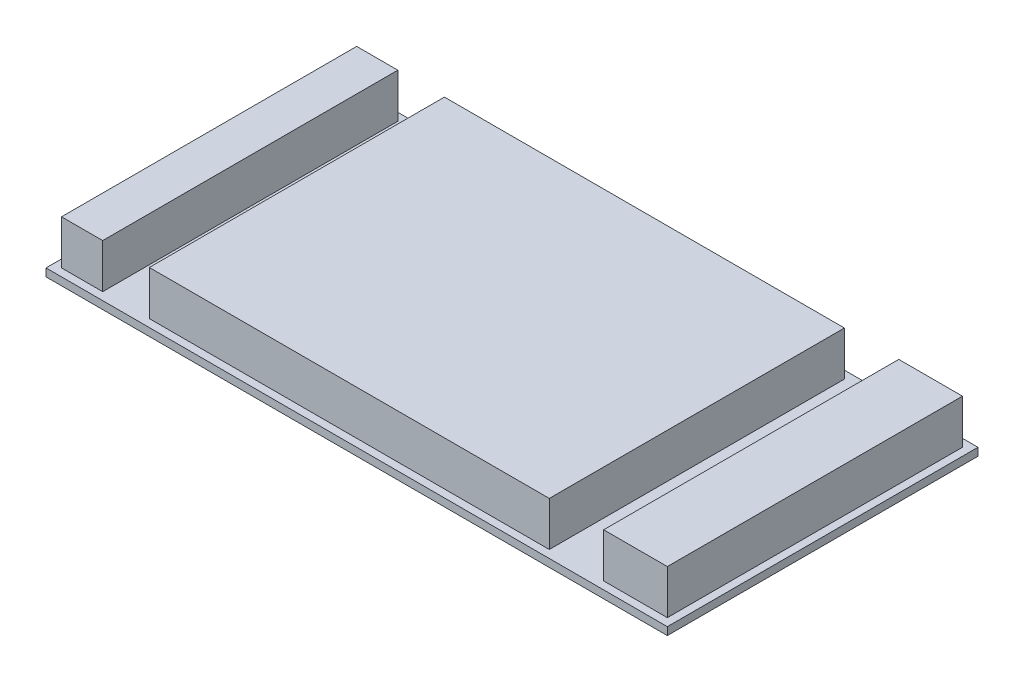
SolidWorks part; units mm, degrees
ref_plane "Front Plane" through (0, 0, 0) normal (0, 0, 1) x (1, 0, 0)
ref_plane "Top Plane" through (0, 0, 0) normal (0, 1, 0) x (1, 0, 0)
ref_plane "Right Plane" through (0, 0, 0) normal (1, 0, 0) x (0, 0, -1)
sketch "Sketch1" plane through (0, 0, 0) normal (0, 1, 0) x (1, 0, 0)
  line L1 (-119.7811, 25.6674) -> (83.4189, 25.6674)
  line L2 (-119.7811, 25.6674) -> (-119.7811, -75.9326)
  line L3 (-119.7811, -75.9326) -> (83.4189, -75.9326)
  line L4 (83.4189, 25.6674) -> (83.4189, -75.9326)
  dimension "D1" = 203.2
  dimension "D2" = 101.6
extrude "Boss-Extrude1" add sketch "Sketch1" along normal blind 2.54
sketch "Sketch2" plane through (0, 2.54, 0) normal (0, 1, 0) x (1, 0, 0)
  line L8 (-117.2411, 23.1274) -> (-117.2411, -73.3926)
  line L9 (-117.2411, -73.3926) -> (80.8789, -73.3926)
  line L10 (80.8789, -73.3926) -> (80.8789, 23.1274)
  line L11 (80.8789, 23.1274) -> (-117.2411, 23.1274)
  line L12 (-117.2411, 23.1274) -> (-117.2411, -73.3926)
  line L13 (-117.2411, -73.3926) -> (80.8789, -73.3926)
  line L14 (80.8789, -73.3926) -> (80.8789, 23.1274)
  line L15 (80.8789, 23.1274) -> (-117.2411, 23.1274)
  dimension "D1" = 2.54
extrude "Boss-Extrude2" add sketch "Sketch2" along normal blind 14.478 contours L12 L13 L14 L15
sketch "Sketch4" plane through (0, 0, -23.1274) normal (0, 0, -1) x (-1, 0, 0)
  line L0 (-60.0509, 17.018) -> (-60.0509, 2.54)
  line L1 (-80.8789, 17.018) -> (117.2411, 17.018) construction
  line L2 (-83.4189, 2.54) -> (119.7811, 2.54) construction
  line L3 (-42.2709, 17.018) -> (-42.2709, 2.54)
  line L4 (-80.8789, 2.54) -> (117.2411, 2.54) construction
  line L5 (-60.0509, 17.018) -> (-42.2709, 17.018)
  line L6 (103.7791, 17.018) -> (103.7791, 2.54)
  line L7 (88.5391, 17.018) -> (88.5391, 2.54)
  line L8 (88.5391, 17.018) -> (103.7791, 17.018)
  line L9 (-60.0509, 2.54) -> (-42.2709, 2.54)
  line L10 (88.5391, 2.54) -> (103.7791, 2.54)
  dimension "D1" = 20.828
  dimension "D2" = 17.78
  dimension "D3" = 13.462
  dimension "D4" = 15.24
extrude "Cut-Extrude6" cut sketch "Sketch4" against normal blind 101.6
